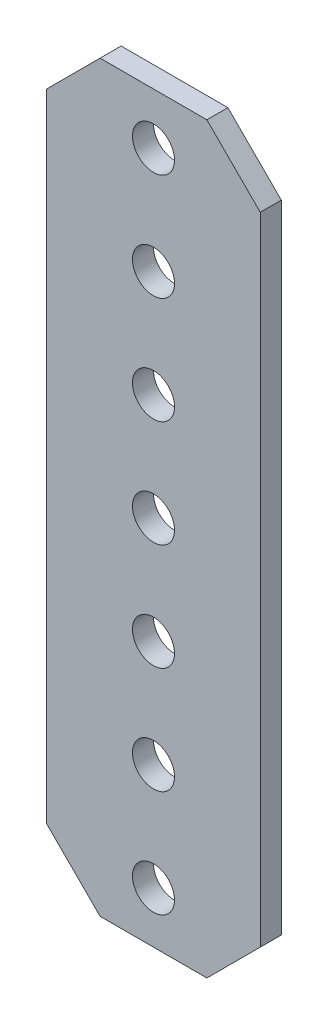
SolidWorks part; units mm, degrees
material "5052-H32"
ref_plane "Front Plane" through (0, 0, 0) normal (0, 0, 1) x (1, 0, 0)
ref_plane "Top Plane" through (0, 0, 0) normal (0, 1, 0) x (1, 0, 0)
ref_plane "Right Plane" through (0, 0, 0) normal (1, 0, 0) x (0, 0, -1)
ref_plane "Plane1" through (0, 0, 1.25) normal (0, 0, 1) x (1, 0, 0)
sketch "Sketch1" plane through (0, 0, 1.25) normal (0, 0, 1) x (1, 0, 0)
  line L0 (-12.7, 37.846) -> (-12.7, -37.846)
  line L1 (-12.7, -37.846) -> (-6.35, -44.196)
  line L2 (-6.35, -44.196) -> (6.35, -44.196)
  line L3 (6.35, -44.196) -> (12.7, -37.846)
  line L4 (12.7, -37.846) -> (12.7, 37.846)
  line L5 (12.7, 37.846) -> (6.35, 44.196)
  line L6 (6.35, 44.196) -> (-6.35, 44.196)
  line L7 (-6.35, 44.196) -> (-12.7, 37.846)
  circle A0 centre (0, -38.1) radius 2.5
  circle A1 centre (0, -25.4) radius 2.5
  circle A2 centre (0, -12.7) radius 2.5
  circle A3 centre (0, 0) radius 2.5
  circle A4 centre (0, 12.7) radius 2.5
  circle A5 centre (0, 38.1) radius 2.5
  circle A6 centre (0, 25.4) radius 2.5
  point P22 (32.731, -44.6331)
  point P23 (0, 0)
  dimension "D1" = 5
  dimension "D2" = 5
  dimension "D3" = 5
  dimension "D4" = 5
  dimension "D5" = 5
  dimension "D6" = 5
  dimension "D7" = 5
  dimension "D8" = 6.35
  dimension "D9" = 12.7
  dimension "D10" = 19.05
  dimension "D11" = 25.4
  dimension "D12" = 6.096
  dimension "D13" = 6.35
  dimension "D14" = 18.796
  dimension "D15" = 31.496
  dimension "D16" = 44.196
  dimension "D17" = 56.896
  dimension "D18" = 69.596
  dimension "D19" = 82.042
  dimension "D20" = 82.296
  dimension "D21" = 88.392
extrude "Boss-Extrude1" add sketch "Sketch1" against normal blind 2.5
